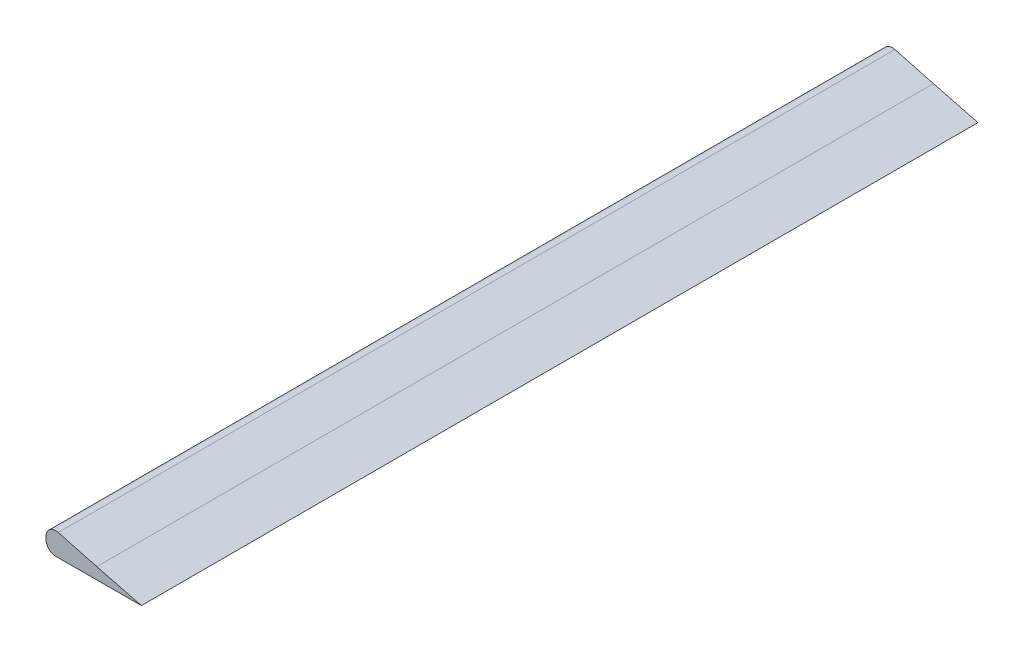
SolidWorks part; units mm, degrees
ref_plane "Front Plane" through (0, 0, 0) normal (0, 0, 1) x (1, 0, 0)
ref_plane "Top Plane" through (0, 0, 0) normal (0, 1, 0) x (1, 0, 0)
ref_plane "Right Plane" through (0, 0, 0) normal (1, 0, 0) x (0, 0, -1)
sketch "Sketch1" plane through (0, 0, 0) normal (0, 0, 1) x (1, 0, 0)
  line L0 (-16.5077, 2.3643) -> (-16.5077, 1.474)
  line L11 (17.3582, -1.9661) -> (1.5352, 2.1042)
  arc A0 (-13.0015, -2.026) -> (-16.5077, 1.474) centre (-13.0077, 1.474) cw
  arc A1 (-12.142, 5.7555) -> (-16.5077, 2.3643) centre (-13.0077, 2.3643) ccw
  spline S6 degree 3 poles (-13.0015, -2.026) (-8.3331, -2.0178) (-3.6646, -2.0095) (1.0038, -2.0006) knots 0.95339 0.95339 0.95339 0.95339 1 1 1 1
  spline S7 degree 3 poles (1.0038, -2.0006) (6.4553, -1.9902) (11.9068, -1.979) (17.3582, -1.9661) knots 1 1 1 1 1.054429 1.054429 1.054429 1.054429
  spline S8 degree 3 poles (1.5352, 2.1042) (-1.4895, 2.9339) (-6.0376, 4.1773) (-10.6083, 5.364) (-12.142, 5.7555) knots 0 0 0 0 0.03125 0.047001 0.047001 0.047001 0.047001
extrude "Boss-Extrude1" add sketch "Sketch1" along normal blind 297
sketch "Sketch2" plane through (0, 1.9191, 0) normal (0, -1, 0) x (1, 0, 0)
  line L0 (-16.5077, 297) -> (-16.5077, 0) construction
  line L1 (-16.5077, 236) -> (-4.5077, 236)
  line L2 (-16.5077, 236) -> (-16.5077, 248)
  line L3 (-16.5077, 248) -> (-4.5077, 248)
  line L4 (-4.5077, 236) -> (-4.5077, 248)
  line L5 (-17.5077, 236) -> (-29.5077, 236) construction
  line L6 (-29.5077, 248) -> (-17.5077, 248) construction
  line L7 (-17.5077, 49) -> (-29.5077, 49) construction
  line L8 (-16.5077, 49) -> (-4.5077, 49)
  line L9 (-16.5077, 49) -> (-16.5077, 61)
  line L10 (-16.5077, 61) -> (-4.5077, 61)
  line L11 (-4.5077, 49) -> (-4.5077, 61)
  line L12 (-29.5077, 61) -> (-21.5077, 61) construction
  dimension "D1" = 0
  dimension "D2" = 0
  dimension "D3" = 12
  dimension "D4" = 0
  dimension "D5" = 0
  dimension "D6" = 12
extrude "Cut-Extrude1" cut sketch "Sketch2" along normal through all
